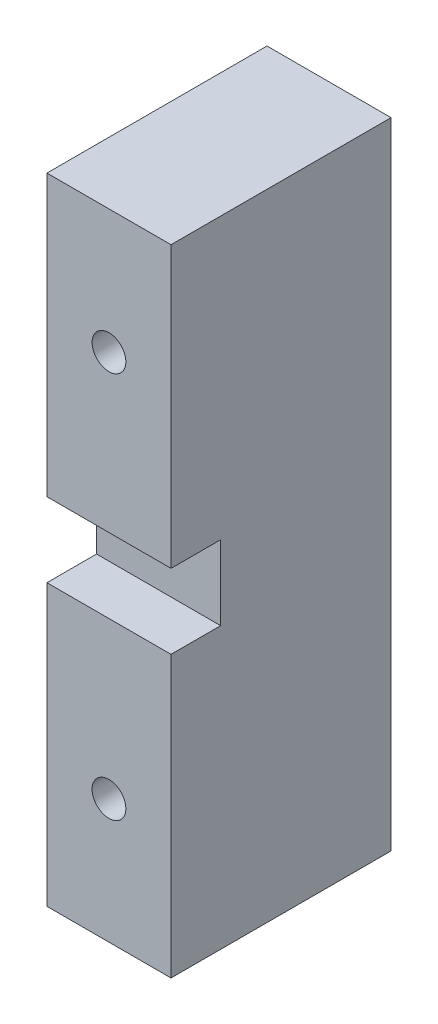
SolidWorks part; units mm, degrees
ref_plane "Plano frontal" through (0, 0, 0) normal (0, 0, 1) x (1, 0, 0)
ref_plane "Plano superior" through (0, 0, 0) normal (0, 1, 0) x (1, 0, 0)
ref_plane "Plano direito" through (0, 0, 0) normal (1, 0, 0) x (0, 0, -1)
ref_plane "Plano1" through (12.7, 0, 0) normal (1, 0, 0) x (0, 0, -1)
sketch "Esboço1" plane through (12.7, 0, 0) normal (1, 0, 0) x (0, 0, -1)
  line L0 (0, 65) -> (-22.5248, 65)
  line L1 (-22.5248, 65) -> (-22.5248, 0)
  line L2 (-22.5248, 0) -> (0, 0)
  line L3 (0, 0) -> (0, 65)
extrude "Ressalto-extrusão1" add sketch "Esboço1" against normal blind 12.7
sketch "Esboço2" plane through (0, 0, 0) normal (-1, 0, 0) x (0, 0, 1)
  line L0 (22.5248, 28.69) -> (22.5248, 36.31)
  line L1 (22.5248, 36.31) -> (17.4448, 36.31)
  line L2 (17.4448, 36.31) -> (17.4448, 28.69)
  line L3 (17.4448, 28.69) -> (22.5248, 28.69)
extrude "Corte-extrusão1" cut sketch "Esboço2" against normal through all
hole_wizard "Furo com folga de M31" positions "Esboço4" profile "Esboço3" hole size "M3" standard "Ansi Metric"
sketch "Esboço4" plane through (0, 0, 0) normal (0, 0, -1) x (-1, 0, 0)
  point P0 (-6.35, 12.7)
  point P1 (-6.35, 52.3)
sketch "Esboço3" plane through (6.35, 12.7, 0) normal (1, 0, 0) x (0, 1, 0)
  line L0 (0, 0) -> (0, 22.5248)
  line L1 (0, 22.5248) -> (1.7272, 22.5248)
  line L2 (1.7272, 22.5248) -> (1.7272, 0)
  line L5 (1.7272, 0) -> (0, 0)
  line L11 (0, -6.35) -> (0, 107.95) construction
  dimension "Thru Hole Dia." = 3.4544
  dimension "Thru Hole Depth" = 22.5248
